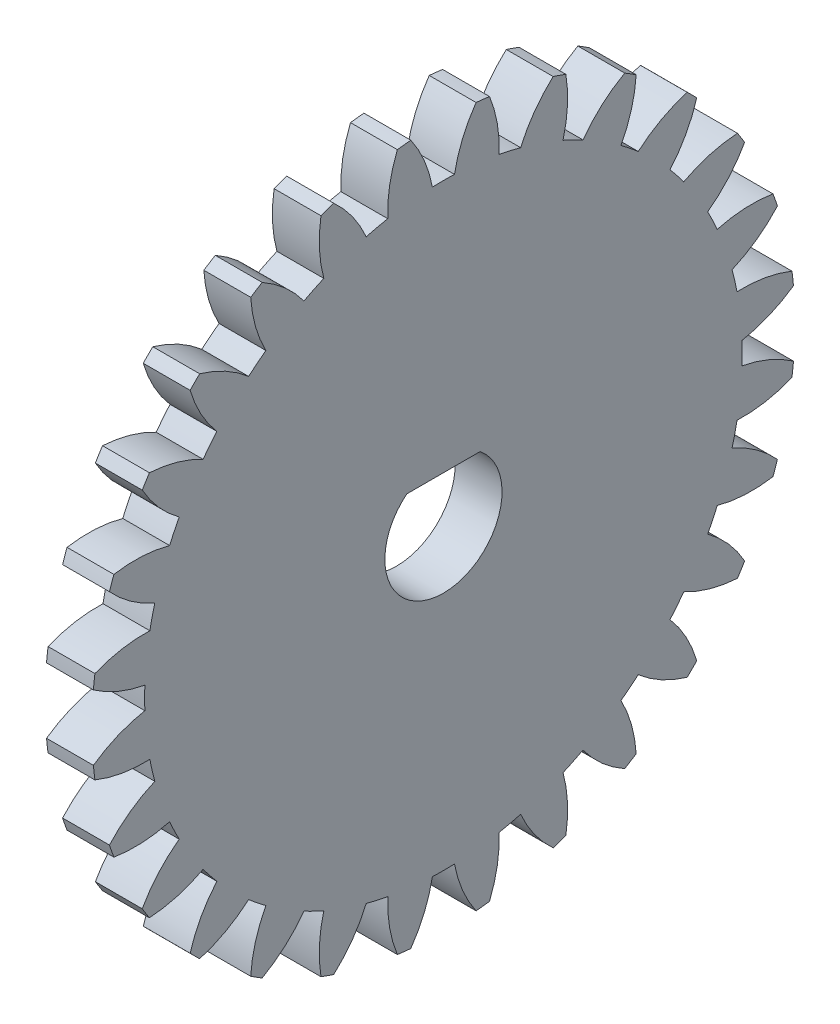
SolidWorks part; units mm, degrees
ref_plane "Plane1" through (0, 0, 0) normal (0, 0, 1) x (1, 0, 0)
ref_plane "Plane2" through (0, 0, 0) normal (0, 1, 0) x (1, 0, 0)
ref_plane "Plane3" through (0, 0, 0) normal (1, 0, 0) x (0, 0, -1)
sketch "HoldingSke" plane through (0, 0, 0) normal (0, 1, 0) x (1, 0, 0)
  line L0 (0, 0) -> (0.8829, -0.4695)
  line L1 (-15, 0) -> (100, 0) construction
  line L2 (0, 0) -> (-2.1039, 2.3779)
  line L3 (0, 0) -> (-11.863, 4.5341)
  line L4 (0, 0) -> (7.6251, 4.0544)
  line L5 (0, 0) -> (-46.8476, -17.4728)
  line L6 (0, 0) -> (-1.6579, -1.1186)
  line L7 (-2.1039, 2.3779) -> (8.6586, 51.2059)
  line L8 (-76.2, 54.61) -> (-75.7, 54.61)
  line L9 (-71.009, 38.7566) -> (-53.1078, 45.2721)
  line L10 (-76.2, 71.12) -> (104.1128, 71.12)
  line L11 (0, 0) -> (-2, 0)
  line L12 (-76.2, 101.6) -> (-76.162, 101.6)
  line L13 (24.9733, 27.94) -> (52.9518, 28.4284)
  line L14 (24.9733, 27.94) -> (24.9743, 27.94)
  line L15 (24.9733, 27.94) -> (100.4006, 29.5858)
  line L16 (-63.627, -1) -> (-12.827, -1)
  circle A0 centre (0, 0) radius 1.5
  circle A1 centre (0, 0) radius 12.749
  circle A2 centre (0, 0) radius 37.5
  circle A3 centre (0, 0) radius 1.5
  dimension "MHD" = 25.498
  dimension "Hub_dia" = 75
  dimension "Bore" = 3
  dimension "MBD" = 3
  dimension "Num_teeth" = 28
  dimension "Pitch_radius" = 180.3128
  dimension "Pitch" = 1
  dimension "Width" = 2
  dimension "Overall_len" = 50
  dimension "Show_teeth" = 28
  dimension "Thickness" = 2
  dimension "OAL" = 50.0001
  dimension "T_dim" = 0.5
  dimension "Ap" = 20
  dimension "H" = 19.05
  dimension "Backlash" = 0.038
  dimension "Addendum_fac" = 1
  dimension "Dedendum_fac" = 1.25
  dimension "Clearance_fac" = 0.25
  dimension "Dedendum_add" = 0.001
  dimension "Module" = 1
sketch "BasProSke" plane through (0, 0, 0) normal (0, 1, 0) x (1, 0, 0)
  line L0 (-10, 0) -> (60, 0) construction
  line L1 (0, 0) -> (0, 15)
  line L2 (0, 0) -> (2, 0)
  line L3 (2, 0) -> (2, 15)
  line L4 (2, 15) -> (0, 15)
  dimension "Diameter" = 30
  dimension "Thickness" = 2
revolve "Base-Revolve" add sketch "BasProSke" angle 360 about L0
sketch "TooCutSke" plane through (0, 0, 0) normal (1, 0, 0) x (0, 0, -1)
  line L1 (0, 0) -> (0, 107) construction
  line L2 (0, 0) -> (-0.8515, 13.9741) construction
  line L3 (0, 0) -> (-3.1309, 27.7873) construction
  line L4 (-0.8515, 13.9741) -> (-1.5654, 13.8936) construction
  arc A0 (0.4713, 12.7403) -> (-0.4713, 12.7403) centre (0, 0) ccw
  arc A1 (1.4098, 14.9591) -> (-1.4098, 14.9591) centre (0, 0) ccw
  circle A2 centre (0, 0) radius 14 construction
  circle A3 centre (0, 0) radius 13.1557 construction
  arc A4 (-0.4713, 12.7403) -> (-1.4098, 14.9591) centre (-5.9775, 11.7193) ccw
  arc A5 (1.4098, 14.9591) -> (0.4713, 12.7403) centre (5.9775, 11.7193) ccw
  dimension "Root_dia" = 25.498
  dimension "Overcut_dia" = 30.0508
  dimension "Pitch_dia" = 28
  dimension "Base_dia" = 26.3114
  dimension "Flank_rad" = 5.6
  dimension "Half_ang" = 6.429
  dimension "Half_CT" = 0.7185
extrude "ToothCut" cut sketch "TooCutSke" along normal through all
fillet "Breaks" [suppressed] radius 0.02
fillet "RootFillets" [suppressed] radius 0.251
pattern_circular "TeethCuts" count 28 every 12.857 about axis through (-10, 0, 0) along (1, 0, 0) of "ToothCut", "RootFillets", "Breaks"
sketch "HubNeaOneSke" plane through (0, 0, 0) normal (-1, 0, 0) x (0, 0, 1)
  circle A0 centre (0, 0) radius 12.749
  dimension "Diameter" = 25.498
extrude "HubNearOne" [suppressed] add sketch "HubNeaOneSke" along normal blind 48.0001
sketch "HubNeaBotSke" plane through (0, 0, 0) normal (-1, 0, 0) x (0, 0, 1)
  circle A0 centre (0, 0) radius 12.749
  dimension "Diameter" = 25.498
extrude "HubNearBoth" [suppressed] add sketch "HubNeaBotSke" along normal blind 24
ref_plane "FarPln" through (2, 0, 0) normal (1, 0, 0) x (0, 0, -1)
sketch "HubFarSke" plane through (2, 0, 0) normal (1, 0, 0) x (0, 0, -1)
  circle A0 centre (0, 0) radius 12.749
  dimension "Diameter" = 25.498
extrude "HubFar" [suppressed] add sketch "HubFarSke" along normal blind 24
sketch "BorSke" plane through (0, 0, 0) normal (1, 0, 0) x (0, 0, -1)
  circle A0 centre (0, 0) radius 1.5
  dimension "Diameter" = 3
extrude "Bore" cut sketch "BorSke" along normal mid plane 100.0001
sketch "KeySke" plane through (0, 0, 0) normal (1, 0, 0) x (0, 0, -1)
  line L0 (-0.6, 0) -> (-0.6, 2)
  line L1 (-0.6, 2) -> (0.6, 2)
  line L2 (0.6, 2) -> (0.6, 0)
  line L3 (0, 0) -> (0, 34) construction
  line L4 (-0.6, 0) -> (0.6, 0)
  dimension "Offset" = 2
  dimension "Width" = 1.2
extrude "Keyway" [suppressed] cut sketch "KeySke" along normal mid plane 100.0001
pattern_circular "Keyway2" [suppressed] count 2 every 90 about axis through (-10, 0, 0) along (1, 0, 0)
sketch "Sketch1" plane through (2, 0, 0) normal (1, 0, 0) x (0, 0, -1)
  line L1 (0, 1.95) -> (1.5644, 1.95)
  line L2 (0, 1.95) -> (-1.5644, 1.95)
  arc A0 (-1.5644, 1.95) -> (1.5644, 1.95) centre (0, 0) ccw
  point P6 (4.1493, 1.95)
extrude "Cut-Extrude1" cut sketch "Sketch1" against normal blind 10
equation "' \"Module@HoldingSke\" = 6.35"
equation "' \"Num_teeth@HoldingSke\" = 12"
equation "' \"Ap@HoldingSke\" =  20"
equation "' \"Width@HoldingSke\" = 0.5 * 25.4"
equation "' \"Hub_dia@HoldingSke\"= 1 * 25.4"
equation "' \"Overall_len@HoldingSke\" = 1.0 * 25.4"
equation "' \"Bore@HoldingSke\" = 0.75 * 25.4"
equation "' \"T_dim@HoldingSke\" = 0.1 * 25.4"
equation "' \"Width@KeySke\" = 0.25 * 25.4"
equation "' \"Show_teeth@HoldingSke\" = 13"
equation "' \"Backlash@HoldingSke\" = 0.009 * 25.4"
equation "' \"Addendum_fac@HoldingSke\" = 1.0"
equation "' \"Dedendum_fac@HoldingSke\" = 1.25"
equation "' \"Dedendum_add@HoldingSke\" = 0.00005 * 25.4"
equation "' \"Clearance_fac@HoldingSke\" = 0.25"
equation "\"Pitch@HoldingSke\" = 1 / \"Module@HoldingSke\""
equation "\"Overcut_dia@TooCutSke\" = (\"Num_teeth@HoldingSke\" + 2 * \"Addendum_fac@HoldingSke\") / \"Pitch@HoldingSke\" + 0.002 * 25.4"
equation "\"Pitch_dia@TooCutSke\" = \"Num_teeth@HoldingSke\" / \"Pitch@HoldingSke\""
equation "\"Base_dia@TooCutSke\" = \"Num_teeth@HoldingSke\" / \"Pitch@HoldingSke\" * cos((\"Ap@HoldingSke\"  * 3.14159265 / 180))"
equation "\"Root_dia@TooCutSke\" = (\"Num_teeth@HoldingSke\" + 2) / \"Pitch@HoldingSke\" - 2 * (\"Addendum_fac@HoldingSke\" + \"Dedendum_fac@HoldingSke\") / \"Pitch@HoldingSke\" - \"Dedendum_add@HoldingSke\" * 2"
equation "\"Half_ang@TooCutSke\" = 180 / \"Num_teeth@HoldingSke\""
equation "\"Half_CT@TooCutSke\" = \"Num_teeth@HoldingSke\" / \"Pitch@HoldingSke\" * sin((3.14159265 / 2 / \"Num_teeth@HoldingSke\")) / 2 - 7 * \"Backlash@HoldingSke\" / 4"
equation "\"Flank_rad@TooCutSke\" = \"Num_teeth@HoldingSke\" / \"Pitch@HoldingSke\" / 5"
equation "\"Radius@RootFillets\" = \"Clearance_fac@HoldingSke\" / \"Pitch@HoldingSke\" + \"Dedendum_add@HoldingSke\""
equation "\"Break_rad@Breaks\" = 0.02 / \"Pitch@HoldingSke\""
equation "\"Thickness@HoldingSke\" = \"Width@HoldingSke\""
equation "\"OAL@HoldingSke\" = \"Thickness@HoldingSke\""
equation "\"MHD@HoldingSke\" = (\"Num_teeth@HoldingSke\" + 2) / \"Pitch@HoldingSke\" - 2 * (\"Addendum_fac@HoldingSke\" + \"Dedendum_fac@HoldingSke\")  / \"Pitch@HoldingSke\" - \"Dedendum_add@HoldingSke\" * 2"
equation "\"MBD@HoldingSke\" = (\"Num_teeth@HoldingSke\" + 2) / \"Pitch@HoldingSke\" - 2 * (\"Addendum_fac@HoldingSke\" + \"Dedendum_fac@HoldingSke\")  / \"Pitch@HoldingSke\" - \"Dedendum_add@HoldingSke\" * 2 - 0.002 * 25.4"
equation "\"MHD@HoldingSke\" = ((sgn( \"MHD@HoldingSke\" - \"Hub_dia@HoldingSke\" )-1)*( \"MHD@HoldingSke\" - \"Hub_dia@HoldingSke\" ))/-2+ \"Hub_dia@HoldingSke\""
equation "\"MBD@HoldingSke\" = ((sgn( \"MBD@HoldingSke\" - \"Bore@HoldingSke\" )-1)*( \"MBD@HoldingSke\" - \"Bore@HoldingSke\" ))/-2+ \"Bore@HoldingSke\""
equation "\"OAL@HoldingSke\" = ((sgn( \"OAL@HoldingSke\" - \"Overall_len@HoldingSke\" )+1)*( \"OAL@HoldingSke\" - \"Overall_len@HoldingSke\" ))/2 + \"Overall_len@HoldingSke\" + 0.000002 * 25.4"
equation "\"Num_teeth@TeethCuts\" = int( \"Show_teeth@HoldingSke\" ) + 1"
equation "\"Num_teeth@TeethCuts\" = ((sgn( \"Num_teeth@TeethCuts\" - \"Num_teeth@HoldingSke\" )-1)*( \"Num_teeth@TeethCuts\" - \"Num_teeth@HoldingSke\" ))/-2+ \"Num_teeth@HoldingSke\""
equation "\"Num_teeth@TeethCuts\" = ((sgn( \"Num_teeth@TeethCuts\" - 2.0)+1)*( \"Num_teeth@TeethCuts\" - 2.0))/2 +2.0"
equation "\"Angle@TeethCuts\" = 360.0 / \"Num_teeth@HoldingSke\""
equation "\"Diameter@BasProSke\" = (\"Num_teeth@HoldingSke\" + 2 * \"Addendum_fac@HoldingSke\") / \"Pitch@HoldingSke\""
equation "\"Thickness@BasProSke\"  = \"Thickness@HoldingSke\""
equation "' \"Fillet_rad@BasProSke\" =  \"Thickness@HoldingSke\" * 0.05"
equation "\"MHD@HoldingSke\" = ((sgn( \"MHD@HoldingSke\" - \"Root_dia@TooCutSke\" )-1)*( \"MHD@HoldingSke\" - \"Root_dia@TooCutSke\" ))/-2+ \"Root_dia@TooCutSke\""
equation "\"Diameter@HubNeaOneSke\" = \"MHD@HoldingSke\""
equation "\"Length@HubNearOne\" = \"OAL@HoldingSke\" - \"Thickness@BasProSke\""
equation "\"Diameter@HubNeaBotSke\" = \"MHD@HoldingSke\""
equation "\"Length@HubNearBoth\" = ( \"OAL@HoldingSke\" - \"Thickness@BasProSke\" ) / 2.0"
equation "\"Thickness@FarPln\" = \"Thickness@BasProSke\""
equation "\"Diameter@HubFarSke\" = \"MHD@HoldingSke\""
equation "\"Length@HubFar\" = ( \"OAL@HoldingSke\" - \"Thickness@BasProSke\" ) / 2.0"
equation "\"Diameter@BorSke\" = \"MBD@HoldingSke\""
equation "\"D1@Bore\" = \"OAL@HoldingSke\" * 2.0"
equation "\"D1@Keyway\" = \"OAL@HoldingSke\" * 2.0"
equation "\"Offset@KeySke\" = \"T_dim@HoldingSke\" + \"MBD@HoldingSke\" / 2.0"
